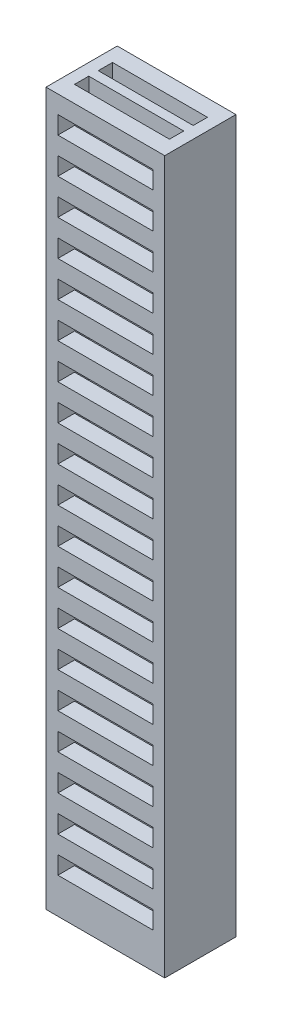
SolidWorks part; units mm, degrees
ref_plane "Front Plane" through (0, 0, 0) normal (0, 0, 1) x (1, 0, 0)
ref_plane "Top Plane" through (0, 0, 0) normal (0, 1, 0) x (1, 0, 0)
ref_plane "Right Plane" through (0, 0, 0) normal (1, 0, 0) x (0, 0, -1)
sketch "Sketch1" plane through (0, 0, 0) normal (0, 1, 0) x (1, 0, 0)
  line L1 (-2.5, -1.5) -> (2.5, -1.5)
  line L2 (-2.5, -1.5) -> (-2.5, 1.5)
  line L3 (-2.5, 1.5) -> (2.5, 1.5)
  line L4 (2.5, -1.5) -> (2.5, 1.5)
  line L5 (-2.5, -1.5) -> (2.5, 1.5) construction
  line L6 (-2.5, 1.5) -> (2.5, -1.5) construction
  point P0 (0, 0)
  dimension "D1" = 5
  dimension "D2" = 3
extrude "Boss-Extrude1" add sketch "Sketch1" along normal mid plane 30
sketch "Sketch2" plane through (0, 15, 0) normal (0, 1, 0) x (1, 0, 0)
  line L0 (-2.5, 1.5) -> (-2.5, -1.5) construction
  line L1 (-2, 0.2) -> (2, 0.2)
  line L2 (-2, 0.2) -> (-2, 0.8)
  line L3 (-2, 0.8) -> (2, 0.8)
  line L4 (2, 0.2) -> (2, 0.8)
  line L5 (-2, 0.2) -> (2, 0.8) construction
  line L6 (-2, 0.8) -> (2, 0.2) construction
  point P0 (0, 0.5)
  dimension "D1" = 0.6
  dimension "D2" = 0.5
  dimension "D3" = 0
  dimension "D4" = 0.5
extrude "Cut-Extrude1" cut sketch "Sketch2" against normal through all and the other way through all
mirror "Mirror1" about plane through (0, 0, 0) normal (0, 0, 1) of "Cut-Extrude1"
sketch "Sketch3" plane through (0, 0, 1.5) normal (0, 0, 1) x (1, 0, 0)
  line L0 (0, -1.65) -> (0, 1.65) construction
  line L1 (-2, 13.5) -> (2, 13.5)
  line L2 (-2, 13.5) -> (-2, 14.25)
  line L3 (-2, 14.25) -> (2, 14.25)
  line L4 (2, 13.5) -> (2, 14.25)
  line L5 (-2, 13.5) -> (2, 14.25) construction
  line L6 (-2, 14.25) -> (2, 13.5) construction
  line L7 (-2.5, 15) -> (2.5, 15) construction
  line L8 (2.5, 15) -> (2.5, -15) construction
  point P0 (0, 13.875)
  dimension "D1" = 0.75
  dimension "D2" = 0.75
  dimension "D3" = 0.5
extrude "Cut-Extrude2" cut sketch "Sketch3" against normal up to next (0.7 mm away)
pattern_linear "LPattern1" count 19 spacing 1.5 along (0, -1, 0) of "Cut-Extrude2"
mirror "Mirror2" about plane through (0, 0, 0) normal (0, 0, 1) of "LPattern1", "Cut-Extrude2"
